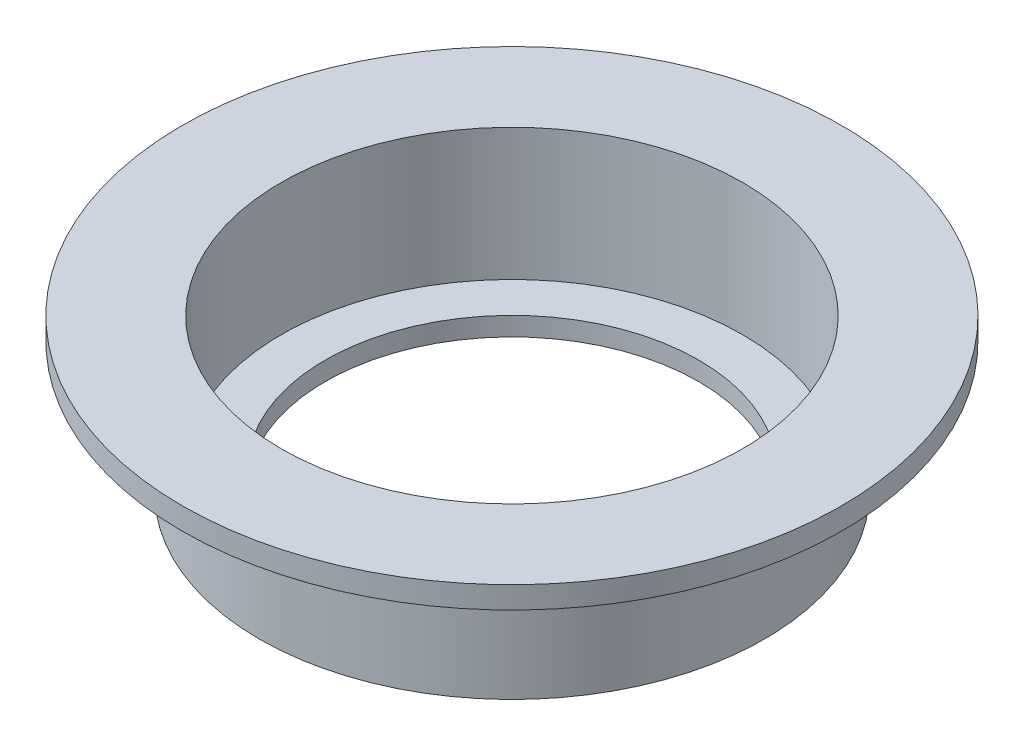
SolidWorks part; units mm, degrees
material "ABS PC"
ref_plane "Front Plane" through (0, 0, 0) normal (0, 0, 1) x (1, 0, 0)
ref_plane "Top Plane" through (0, 0, 0) normal (0, 1, 0) x (1, 0, 0)
ref_plane "Right Plane" through (0, 0, 0) normal (1, 0, 0) x (0, 0, -1)
sketch "Sketch1" plane through (0, 0, 0) normal (0, 0, 1) x (1, 0, 0)
  line L0 (15, 3.175) -> (10.5, 3.175)
  line L1 (15, 3.175) -> (15, 2.175)
  line L2 (15, 2.175) -> (11.5, 2.175)
  line L3 (11.5, 2.175) -> (11.5, -3.825)
  line L4 (11.5, -3.825) -> (10.5, -3.825)
  line L5 (10.5, -3.825) -> (10.5, -3.675)
  line L6 (10.5, -3.675) -> (8.5, -3.675)
  line L7 (8.5, -3.675) -> (8.5, -2.825)
  line L8 (8.5, -2.825) -> (10.5, -2.825)
  line L9 (10.5, 3.175) -> (10.5, -2.825)
  line L10 (0, 11.2232) -> (0, -13.5804) construction
  point P12 (10.5, -3.75)
  dimension "D1" = 21
  dimension "D2" = 1
  dimension "D3" = 17
  dimension "D4" = 30
  dimension "D5" = 1
  dimension "D6" = 1
  dimension "D7" = 0.15
  dimension "D8" = 6
  dimension "D9" = 6
revolve "Revolve1" add sketch "Sketch1" angle 360 about L10
